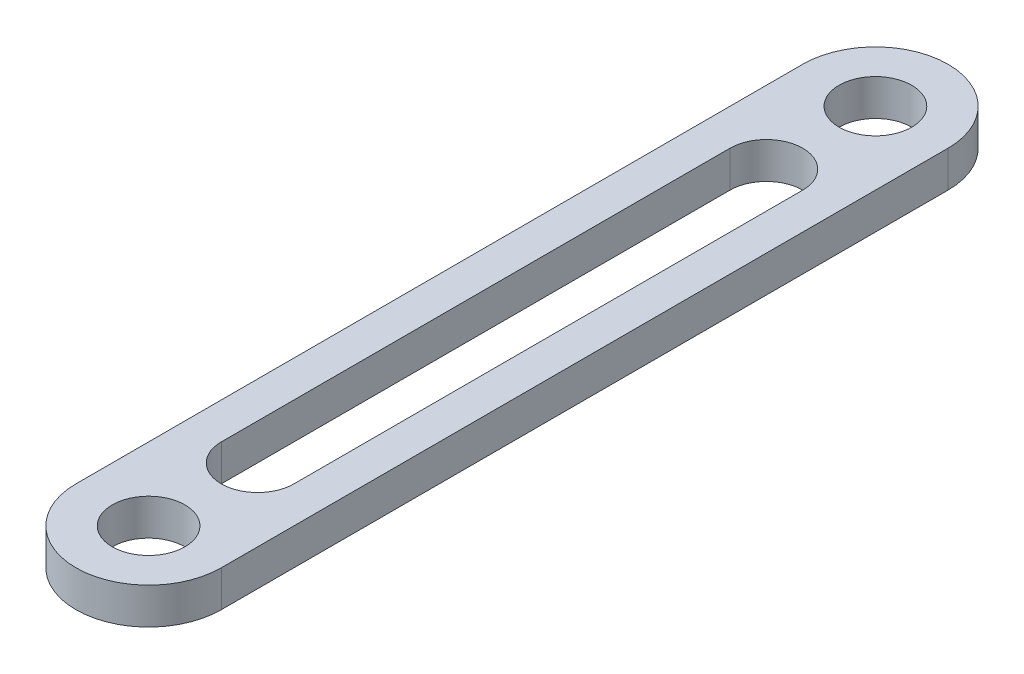
SolidWorks part; units mm, degrees
ref_plane "Front Plane" through (0, 0, 0) normal (0, 0, 1) x (1, 0, 0)
ref_plane "Top Plane" through (0, 0, 0) normal (0, 1, 0) x (1, 0, 0)
ref_plane "Right Plane" through (0, 0, 0) normal (1, 0, 0) x (0, 0, -1)
sketch "Sketch2" plane through (0, 0, 0) normal (0, 1, 0) x (1, 0, 0)
  line L0 (0, 0) -> (0, -100) construction
  line L1 (10, 0) -> (10, -100)
  line L2 (-10, 0) -> (-10, -100)
  line L3 (0, -15) -> (0, -85) construction
  line L4 (5, -15) -> (5, -85)
  line L5 (-5, -15) -> (-5, -85)
  arc A0 (10, 0) -> (-10, 0) centre (0, 0) ccw
  arc A1 (-10, -100) -> (10, -100) centre (0, -100) ccw
  arc A2 (5, -15) -> (-5, -15) centre (0, -15) ccw
  arc A3 (-5, -85) -> (5, -85) centre (0, -85) ccw
  circle A4 centre (0, 0) radius 5
  circle A5 centre (0, -100) radius 5
  point P3 (0, -50)
  point P10 (0, -50)
  dimension "D1" = 10
  dimension "D2" = 100
  dimension "D6" = 10
  dimension "D7" = 10
  dimension "D3" = 10
  dimension "D4" = 15
  dimension "D5" = 70
extrude "Boss-Extrude1" add sketch "Sketch2" along normal blind 5
